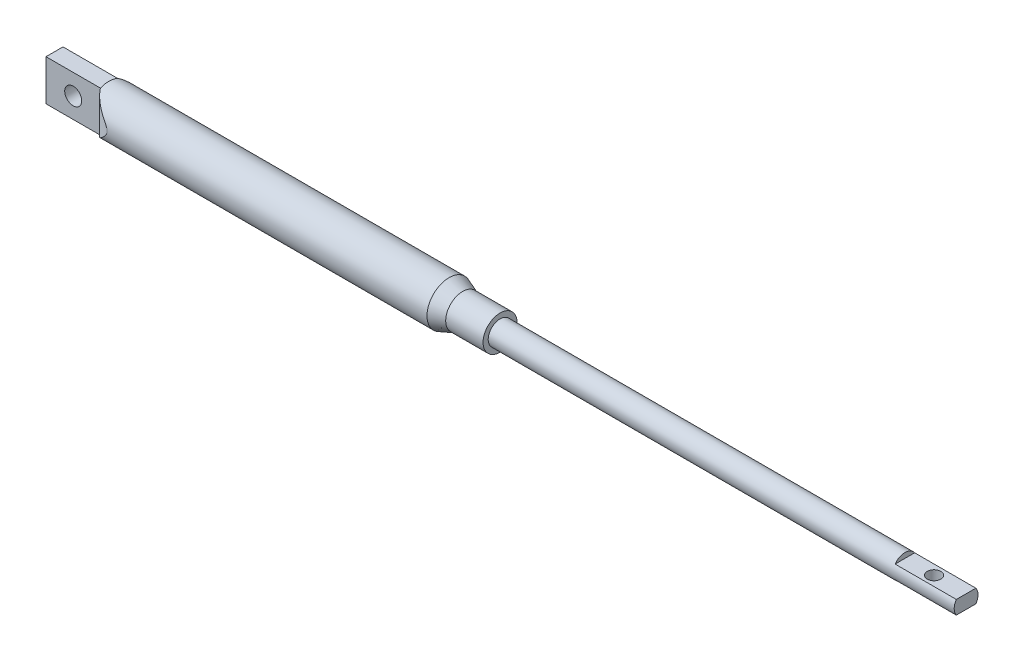
SolidWorks part; units mm, degrees
ref_plane "Front Plane" through (0, 0, 0) normal (0, 0, 1) x (1, 0, 0)
ref_plane "Top Plane" through (0, 0, 0) normal (0, 1, 0) x (1, 0, 0)
ref_plane "Right Plane" through (0, 0, 0) normal (1, 0, 0) x (0, 0, -1)
sketch "Sketch1" plane through (0, 0, 0) normal (0, 1, 0) x (1, 0, 0)
  line L0 (0, 0) -> (536, 0) construction
  line L1 (0, 0) -> (0, 6.5)
  line L2 (0, 6.5) -> (116, 6.5)
  line L3 (116, 6.5) -> (120, 5)
  line L4 (120, 5) -> (131, 5)
  line L5 (131, 5) -> (131, 3.5)
  line L6 (131, 3.5) -> (268, 3.5)
  line L7 (268, 3.5) -> (268, 0)
  line L8 (0, 0) -> (268, 0)
  dimension "D1" = 116
  dimension "D2" = 15
  dimension "D3" = 4
  dimension "D4" = 13
  dimension "D5" = 10
  dimension "D6" = 7
  dimension "D7" = 137
revolve "Revolve1" add sketch "Sketch1" angle 360 about L0
sketch "Sketch2" plane through (0, 0, 0) normal (0, 1, 0) x (1, 0, 0)
  line L0 (16, 2.5) -> (22, 6.5) construction
  line L1 (-16, 2.5) -> (16, 2.5)
  line L2 (-16, 2.5) -> (-16, -2.5)
  line L3 (-16, -2.5) -> (16, -2.5)
  line L4 (16, 2.5) -> (16, -2.5)
  line L5 (-16, 2.5) -> (16, -2.5) construction
  line L6 (-16, -2.5) -> (16, 2.5) construction
  line L7 (0, 6.5) -> (0, -6.5) construction
  line L8 (116, 6.5) -> (0, 6.5) construction
  line L9 (0, 6.5) -> (0, -6.5)
  line L10 (116, 6.5) -> (0, 6.5)
  line L11 (0, 0) -> (-19.8567, 0) construction
  line L12 (116, -6.5) -> (0, -6.5)
  line L13 (16, -2.5) -> (22, -6.5) construction
  arc A0 (16, 2.5) -> (22, 6.5) centre (23.9566, -2.935) cw
  arc A1 (16, -2.5) -> (22, -6.5) centre (23.9566, 2.935) ccw
  point P0 (0, 0)
  dimension "D1" = 5
  dimension "D2" = 16
  dimension "D3" = 6
  dimension "D4" = 0.7
extrude "Cut-Extrude1" cut sketch "Sketch2" against normal mid plane 42 contours L0 L10 L9 L1 | L13 L3 L9 L12
sketch "Sketch5" plane through (0, 0, -2.5) normal (0, 0, -1) x (-1, 0, 0)
  line L1 (-16, 6) -> (3.3279, 6)
  line L2 (-16, 6) -> (-16, 15.0312)
  line L3 (-16, 15.0312) -> (3.3279, 15.0312)
  line L4 (3.3279, 6) -> (3.3279, 15.0312)
extrude "Cut-Extrude4" cut sketch "Sketch5" against normal blind 25
sketch "Sketch8" plane through (0, 0, 0) normal (0, 0, 1) x (1, 0, 0)
  line L0 (268, -3.5) -> (268, 3.5) construction
  line L1 (286, -2) -> (250, -2)
  line L2 (286, -2) -> (286, 2)
  line L3 (286, 2) -> (250, 2)
  line L4 (250, -2) -> (250, 2)
  line L5 (286, -2) -> (250, 2) construction
  line L6 (286, 2) -> (250, -2) construction
  line L7 (250, 2) -> (250, 7.3747)
  line L8 (250, 7.3747) -> (275.0372, 6.6221)
  line L9 (275.0372, 6.6221) -> (275.0372, -10.2044)
  line L10 (275.0372, -10.2044) -> (250, -8.8066)
  line L11 (250, -8.8066) -> (250, -2)
  point P0 (268, 0)
  dimension "D1" = 18
  dimension "D2" = 4
extrude "Cut-Extrude5" cut sketch "Sketch8" against normal mid plane 10 contours L9 L8 L7 L3 | L11 L10 L9 L1
sketch "Sketch9" plane through (0, 2, 0) normal (0, 1, 0) x (1, 0, 0)
  circle A0 centre (258.568, 0) radius 2
  dimension "D1" = 4
extrude "Cut-Extrude6" cut sketch "Sketch9" against normal blind 10
sketch "Sketch10" plane through (0, 0, 2.5) normal (0, 0, 1) x (1, 0, 0)
  circle A0 centre (8, 0) radius 2.5
  dimension "D1" = 5
  dimension "D2" = 8
extrude "Cut-Extrude7" cut sketch "Sketch10" against normal blind 10
